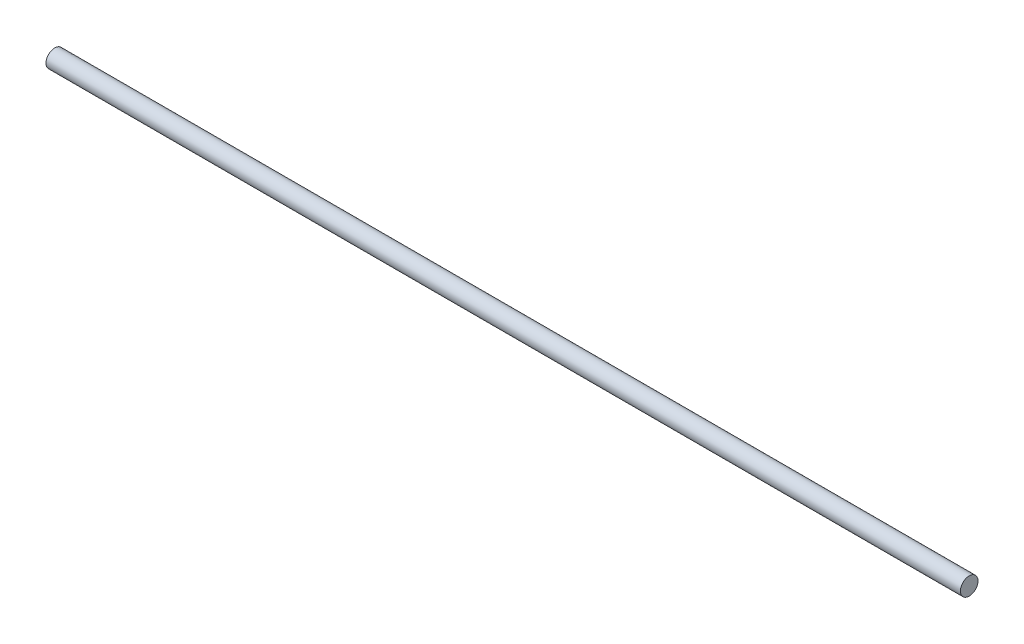
SolidWorks part; units mm, degrees
ref_plane "Front Plane" through (0, 0, 0) normal (0, 0, 1) x (1, 0, 0)
ref_plane "Top Plane" through (0, 0, 0) normal (0, 1, 0) x (1, 0, 0)
ref_plane "Right Plane" through (0, 0, 0) normal (1, 0, 0) x (0, 0, -1)
sketch "Sketch1" plane through (0, 0, 0) normal (1, 0, 0) x (0, 0, -1)
  circle A0 centre (0, 0) radius 5
  dimension "D1" = 10
extrude "Boss-Extrude1" add sketch "Sketch1" along normal mid plane 520
